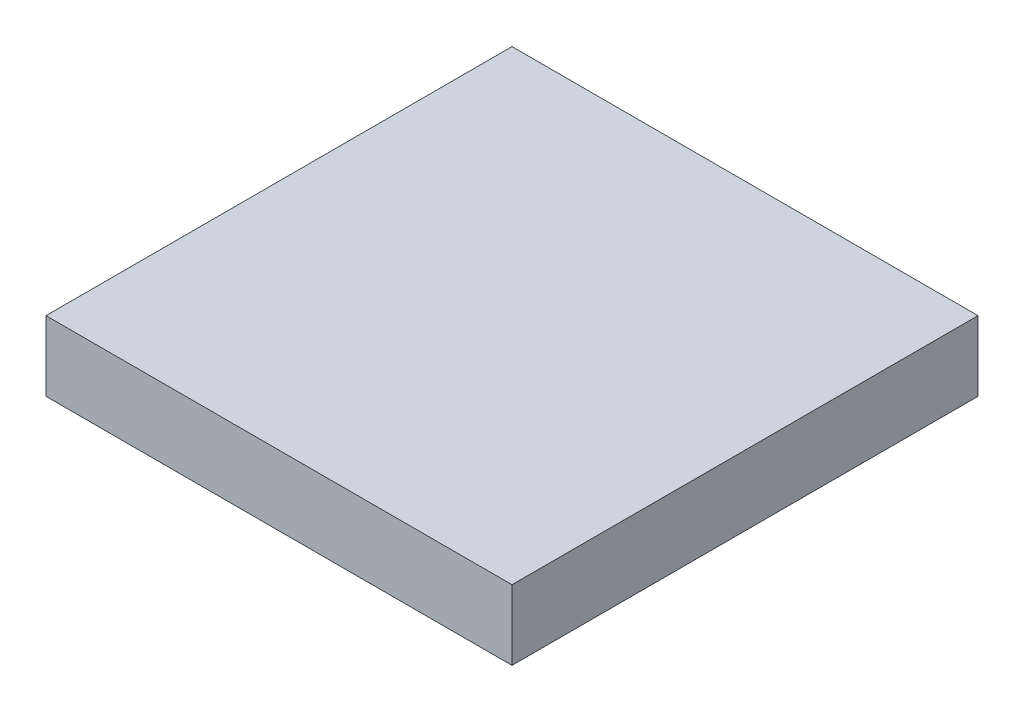
SolidWorks part; units mm, degrees
ref_plane "Front Plane" through (0, 0, 0) normal (0, 0, 1) x (1, 0, 0)
ref_plane "Top Plane" through (0, 0, 0) normal (0, 1, 0) x (1, 0, 0)
ref_plane "Right Plane" through (0, 0, 0) normal (1, 0, 0) x (0, 0, -1)
sketch "Sketch1" plane through (0, 0, 0) normal (0, 1, 0) x (1, 0, 0)
  line L1 (0, 0) -> (100, 0)
  line L2 (0, 0) -> (0, 100)
  line L3 (0, 100) -> (100, 100)
  line L4 (100, 0) -> (100, 100)
  dimension "D1" = 100
  dimension "D2" = 100
extrude "Boss-Extrude1" add sketch "Sketch1" along normal blind 15
